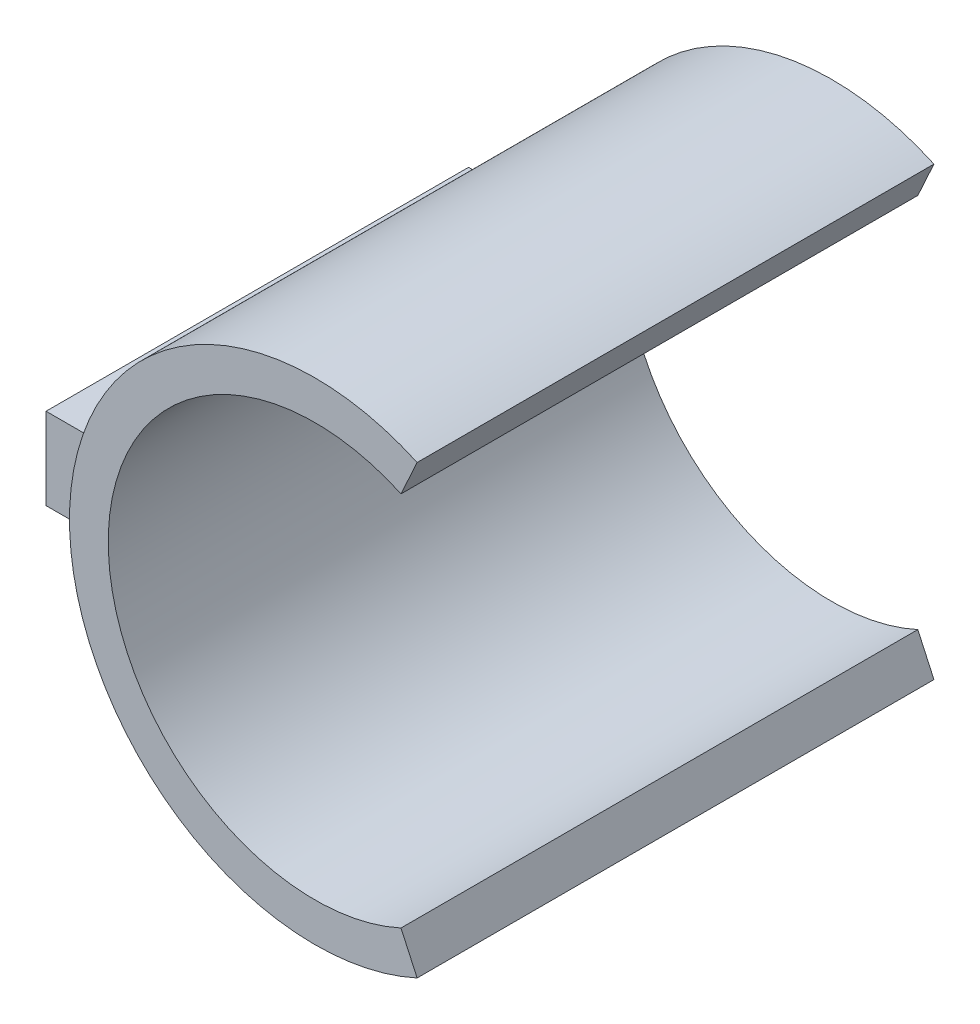
SolidWorks part; units mm, degrees
ref_plane "Front Plane" through (0, 0, 0) normal (0, 0, 1) x (1, 0, 0)
ref_plane "Top Plane" through (0, 0, 0) normal (0, 1, 0) x (1, 0, 0)
ref_plane "Right Plane" through (0, 0, 0) normal (1, 0, 0) x (0, 0, -1)
sketch "Sketch1" plane through (0, 0, 0) normal (0, 0, 1) x (1, 0, 0)
  circle A0 centre (0, 0) radius 4
  circle A1 centre (0, 0) radius 4.75
  dimension "D1" = 8
  dimension "D2" = 9.5
extrude "Boss-Extrude1" add sketch "Sketch1" along normal blind 10
sketch "Sketch3" plane through (0, 0, 10) normal (0, 0, 1) x (1, 0, 0)
  line L0 (0, 0) -> (5.5064, 0) construction
  line L1 (4, 0) -> (4.75, 0)
  line L2 (1.6645, 3.6372) -> (1.9766, 4.3192)
  line L3 (1.6645, -3.6372) -> (1.9766, -4.3192)
  circle A0 centre (0, 0) radius 4 construction
  circle A1 centre (0, 0) radius 4.75
  circle A2 centre (0, 0) radius 4.75
  circle A3 centre (0, 0) radius 4
  arc A4 (4, 0) -> (1.6645, 3.6372) centre (0, 0) ccw
  arc A5 (1.9766, 4.3192) -> (4.75, 0.0148) centre (0, 0) cw
  circle M5 centre (0, 0) radius 4.75
  circle M6 centre (0, 0) radius 4
  dimension "D1" = 0
extrude "Cut-Extrude2" cut sketch "Sketch3" against normal blind 10 contours L2 L1 A2 M6 M5 | L3 L1 M6 M5
ref_plane "Plane1" through (-4.5, 0, 0) normal (1, 0, 0) x (0, 0, -1)
sketch "Sketch4" plane through (-4.5, 0, 0) normal (1, 0, 0) x (0, 0, -1)
  line L1 (-1.0293, 0.7913) -> (-9.2034, 0.7913)
  line L2 (-1.0293, 0.7913) -> (-1.0293, -0.791)
  line L3 (-1.0293, -0.791) -> (-9.2034, -0.791)
  line L4 (-9.2034, 0.7913) -> (-9.2034, -0.791)
  point P5 (-5.1164, -0.791)
  dimension "D1" = 8.1742
  dimension "D2" = 1.5823
  dimension "D3" = 1.0293
  dimension "D4" = 0.7913
extrude "Boss-Extrude2" add sketch "Sketch4" against normal blind 1.5
sketch "Sketch5" plane through (-6, 0, 0) normal (-1, 0, 0) x (0, 0, 1)
  line L4 (9.2034, 0.7913) -> (1.0293, 0.7913)
  line L5 (9.2034, -0.791) -> (9.2034, 0.7913)
  line L6 (1.0293, -0.791) -> (9.2034, -0.791)
  line L7 (1.0293, 0.7913) -> (1.0293, -0.791)
  line L8 (9.2034, 0.7913) -> (1.0293, 0.7913)
  line L9 (9.2034, -0.791) -> (9.2034, 0.7913)
  line L10 (1.0293, -0.791) -> (9.2034, -0.791)
  line L11 (1.0293, 0.7913) -> (1.0293, -0.791)
  point P2 (5.1164, -0.791)
  dimension "D1" = 0
